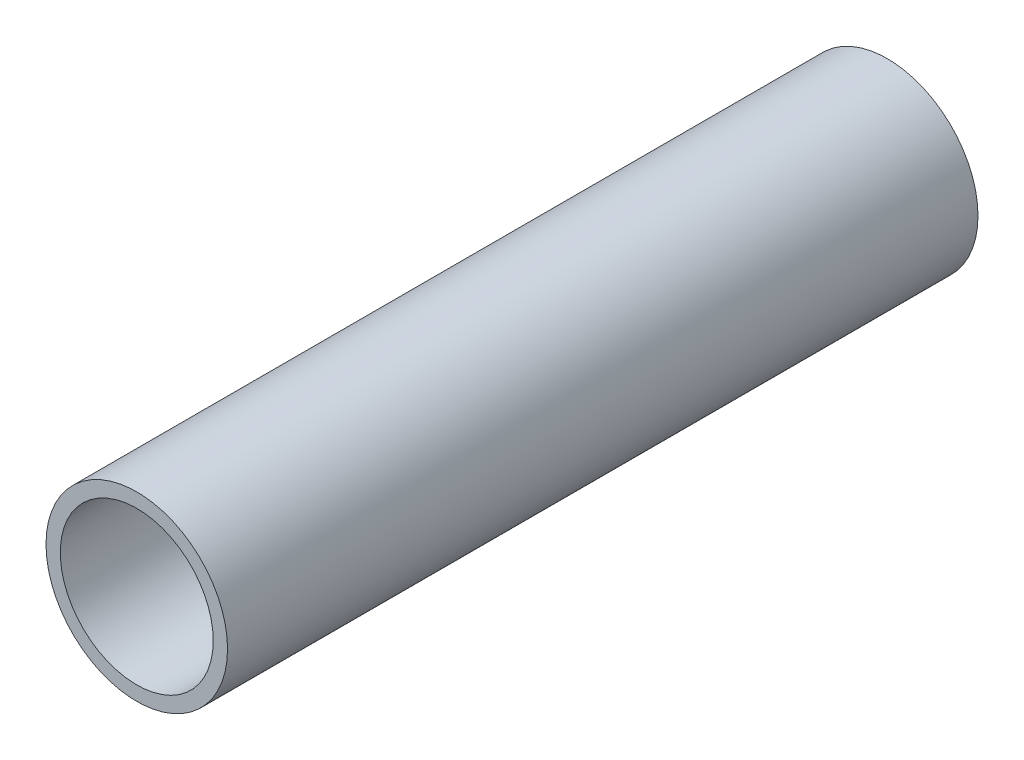
SolidWorks part; units mm, degrees
material "Hexcel AS4C (3000 Filaments)"
ref_plane "Front Plane" through (0, 0, 0) normal (0, 0, 1) x (1, 0, 0)
ref_plane "Top Plane" through (0, 0, 0) normal (0, 1, 0) x (1, 0, 0)
ref_plane "Right Plane" through (0, 0, 0) normal (1, 0, 0) x (0, 0, -1)
sketch "Sketch1" plane through (0, 0, 0) normal (0, 0, 1) x (1, 0, 0)
  circle A0 centre (0, 0) radius 12.7
  circle A1 centre (0, 0) radius 10.7
  dimension "D1" = 25.4
  dimension "D2" = 2
extrude "Boss-Extrude1" add sketch "Sketch1" along normal blind 105
